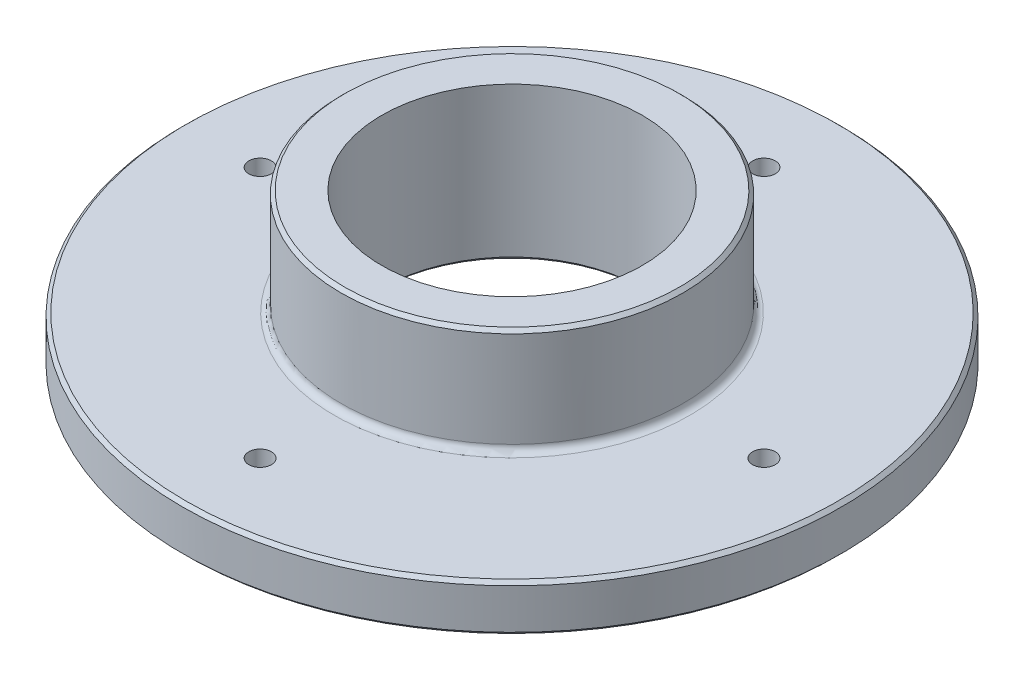
SolidWorks part; units mm, degrees
material "PVC Rígido"
ref_plane "Plano frontal" through (0, 0, 0) normal (0, 0, 1) x (1, 0, 0)
ref_plane "Plano superior" through (0, 0, 0) normal (0, 1, 0) x (1, 0, 0)
ref_plane "Plano direito" through (0, 0, 0) normal (1, 0, 0) x (0, 0, -1)
sketch "Esboço1" plane through (0, 0, 0) normal (0, 0, 1) x (1, 0, 0)
  line L0 (0, 0) -> (0, 77.0025) construction
  line L1 (0, 0) -> (139.5904, 0) construction
  line L2 (96.4, 0) -> (96.4, 13.8)
  line L3 (96.4, 13.8) -> (52, 13.8)
  line L4 (50, 15.8) -> (50, 44.8)
  line L5 (50, 44.8) -> (38.1, 44.8)
  line L6 (38.1, 44.8) -> (38.1, 0)
  line L7 (38.1, 0) -> (96.4, 0)
  arc A0 (52, 13.8) -> (50, 15.8) centre (52, 15.8) cw
  dimension "D6" = 2
  dimension "D1" = 76.2
  dimension "D2" = 192.8
  dimension "D3" = 13.8
  dimension "D4" = 100
  dimension "D5" = 44.8
revolve "Revolução1" add sketch "Esboço1" angle 360 about L0
chamfer "Chanfro1" distance 1 angle 45 4 edges at (0, 13.8, -96.4) (0, 0, -96.4) (0, 0, -38.1) (0, 44.8, -50)
hole_wizard "Furo com folga de M61" positions "Esboço2" profile "Esboço3" hole size "M6" standard "Ansi Metric"
sketch "Esboço2" plane through (0, 13.8, 0) normal (0, 1, 0) x (0, 0, 1)
  line L0 (0, 52) -> (0, 95.4) construction
  circle A2 centre (0, 0) radius 73.7 construction
  point P0 (0, 73.7)
  point P17 (73.7, 0)
  point P18 (0, -73.7)
  point P19 (-73.7, 0)
  point P20 (0, 0)
sketch "Esboço3" plane through (73.7, 13.8, 0) normal (1, 0, 0) x (0, 0, 1)
  line L0 (0, 0) -> (0, 25.7818)
  line L1 (0, 25.7818) -> (3.3, 23.799)
  line L2 (3.3, 23.799) -> (3.3, 0)
  line L3 (3.3, 0) -> (0, 0)
  line L4 (0, 25.7818) -> (-3.3, 23.799) construction
  line L5 (0, -6.35) -> (0, 107.95) construction
  dimension "Hole Dia." = 6.6
  dimension "Hole Depth" = 23.799
  dimension "Drill Angle" = 118
